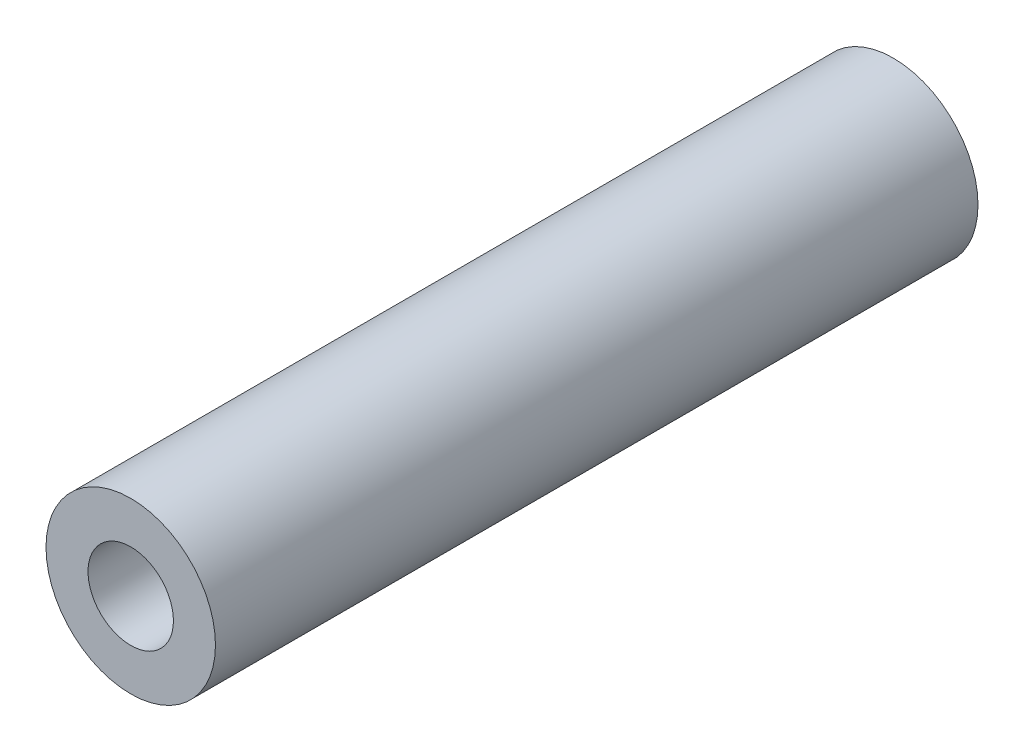
SolidWorks part; units mm, degrees
material "6061-T6 (SS)"
ref_plane "Front Plane" through (0, 0, 0) normal (0, 0, 1) x (1, 0, 0)
ref_plane "Top Plane" through (0, 0, 0) normal (0, 1, 0) x (1, 0, 0)
ref_plane "Right Plane" through (0, 0, 0) normal (1, 0, 0) x (0, 0, -1)
sketch "Sketch1" plane through (0, 0, 0) normal (0, 0, 1) x (1, 0, 0)
  circle A0 centre (0, 0) radius 6.35
  circle A1 centre (0, 0) radius 3.2004
  dimension "OD" = 12.7
  dimension "ID" = 6.4008
extrude "Extrude1" add sketch "Sketch1" along normal mid plane 57.15
sketch "Sketch2" plane through (0, 0, 0) normal (1, 0, 0) x (0, 0, -1)
  line L0 (-28.575, -3.2004) -> (28.575, -3.2004) construction
  line L3 (28.575, 3.2004) -> (-28.575, 3.2004) construction
  line L5 (-28.575, -3.2004) -> (28.575, -3.2004)
  line L6 (28.575, 3.2004) -> (-28.575, 3.2004)
sketch "Sketch4" plane through (0, 0, 28.575) normal (0, 0, 1) x (1, 0, 0)
  line L0 (0, 0) -> (-2.263, 2.263)
  line L1 (0, -55) -> (0, 55) construction
  circle A0 centre (0, 0) radius 3.2004 construction
  dimension "D1" = 45
